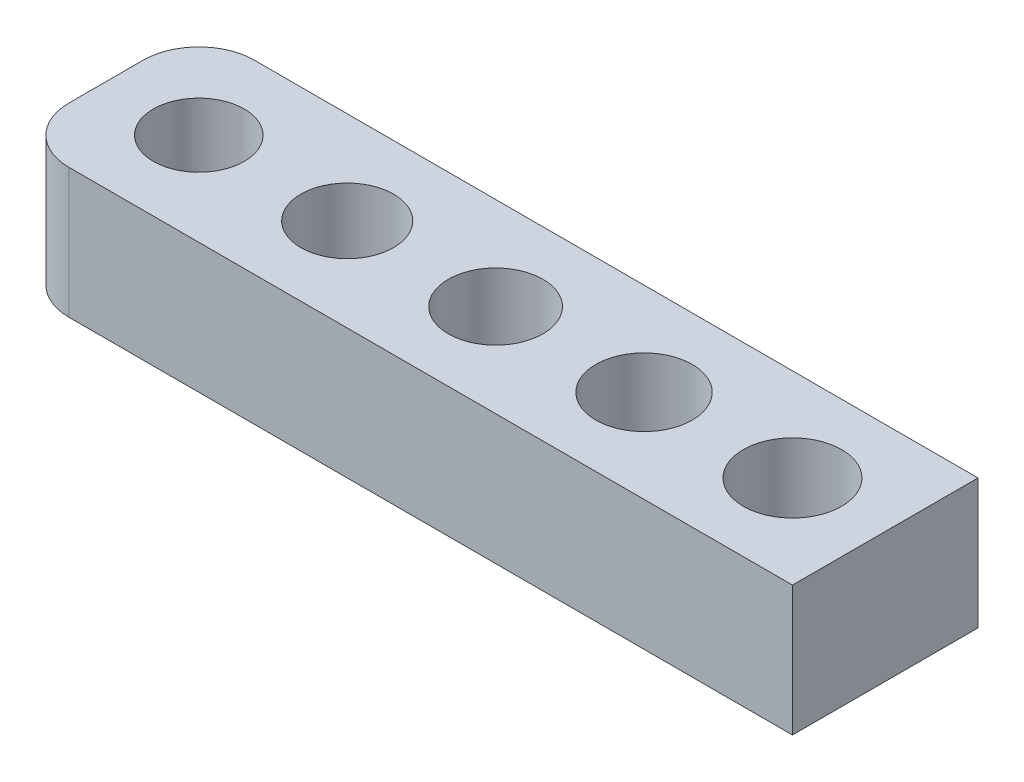
SolidWorks part; units mm, degrees
ref_plane "Front Plane" through (0, 0, 0) normal (0, 0, 1) x (1, 0, 0)
ref_plane "Top Plane" through (0, 0, 0) normal (0, 1, 0) x (1, 0, 0)
ref_plane "Right Plane" through (0, 0, 0) normal (1, 0, 0) x (0, 0, -1)
sketch "Sketch1" plane through (0, 0, 0) normal (0, 1, 0) x (1, 0, 0)
  line L0 (0, 0) -> (50, 0) construction
  line L2 (-5, 5) -> (37, 5)
  line L3 (-5, 5) -> (-5, -5)
  line L4 (-5, -5) -> (37, -5)
  line L5 (37, 5) -> (37, -5)
  line L6 (-5, 5) -> (37, -5) construction
  line L7 (-5, -5) -> (37, 5) construction
  circle A0 centre (0, 0) radius 2.45
  circle A1 centre (8, 0) radius 2.5
  circle A2 centre (16, 0) radius 2.55
  circle A3 centre (24, 0) radius 2.6
  circle A4 centre (32, 0) radius 2.65
  point P16 (0, 0)
  point P17 (0, 0)
  point P18 (-1.3863, 3.8707)
  dimension "D1" = 4.9
  dimension "D2" = 5
  dimension "D3" = 5.1
  dimension "D4" = 5.2
  dimension "D5" = 5.3
  dimension "D6" = 8
  dimension "D7" = 50
  dimension "D8" = 8
  dimension "D9" = 8
  dimension "D10" = 8
  dimension "D11" = 5
  dimension "D12" = 5
extrude "Boss-Extrude1" add sketch "Sketch1" along normal blind 7
fillet "Fillet2" radius 3 2 edges at (-5, 3.5, 5) (-5, 3.5, -5)
